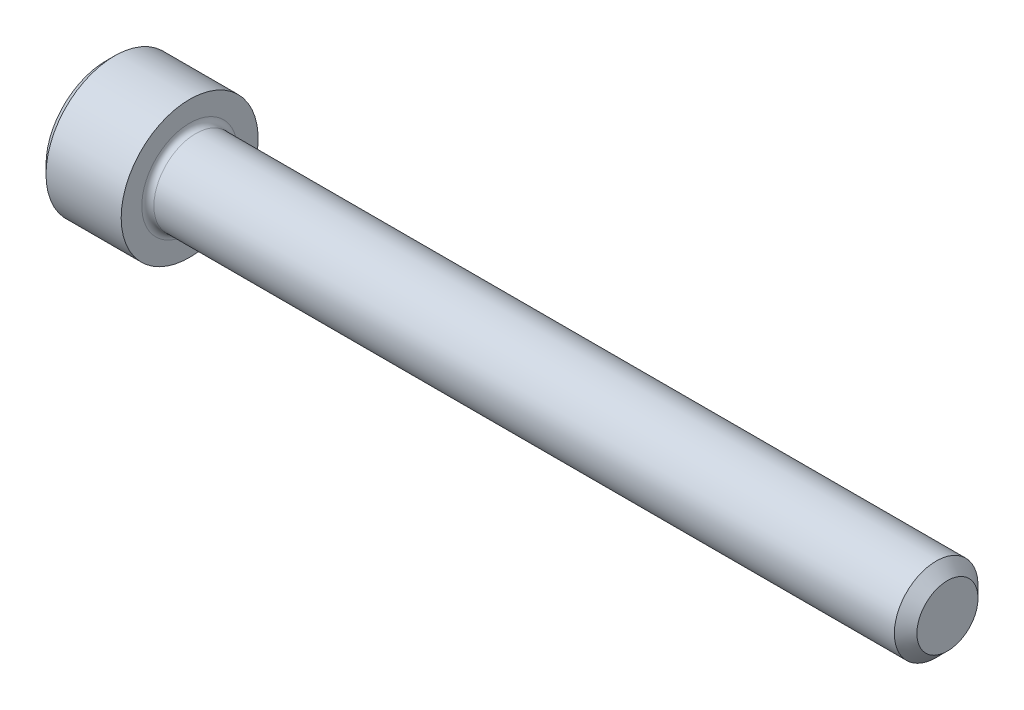
SolidWorks part; units mm, degrees
revolve "Base-Revolve" add sketch "BodySke"
sketch "BodySke" plane through (0, 0, 0) normal (0, 0, 1) x (1, 0, 0)
  line L0 (0, 0) -> (0, 2.5146)
  line L1 (0.3556, 2.8702) -> (3.5052, 2.8702)
  line L2 (3.5052, 2.8702) -> (3.5052, 1.7526)
  line L3 (3.5052, 1.7526) -> (34.7828, 1.7526)
  line L4 (35.2552, 1.2802) -> (35.2552, 0)
  line L5 (35.2552, 0) -> (0, 0)
  line L6 (-31.75, 0) -> (127, 0) construction
  line L7 (0, 2.5146) -> (0.3556, 2.8702)
  line L8 (35.2552, 1.2802) -> (34.7828, 1.7526)
  line L9 (0, -2.5146) -> (0.3556, -2.8702) construction
  line L10 (35.2552, -1.2802) -> (34.7828, -1.7526) construction
  line L11 (4.2977, 9.525) -> (4.2977, 3.175) construction
  line L12 (22.5552, 9.525) -> (22.5552, 3.175) construction
  line L13 (-2.8448, 9.525) -> (-2.8448, 3.175) construction
  dimension "Diameter" = 3.5052
  dimension "Head_ht" = 3.5052
  dimension "Length" = 31.75
  dimension "Body_ch_ang" = 45
  dimension "Head_dia" = 5.7404
  dimension "Head_ch_ang" = 45
  dimension "Head_side_ht" = 3.1496
  dimension "Minor_dia" = 2.5603
  dimension "Advance" = 0.7925
  dimension "Thread_nom" = 12.7
  dimension "Thread_length" = 38.1
cosmetic thread "ThreadCosmetic" [suppressed]
fillet "Fillet1" radius 0.254 1 edges at (3.5052, 0, 1.7526)
ref_plane "Plane1" through (0, 0, 0) normal (0, 0, 1) x (1, 0, 0)
ref_plane "Plane2" through (0, 0, 0) normal (0, 1, 0) x (1, 0, 0)
ref_plane "Plane3" through (0, 0, 0) normal (1, 0, 0) x (0, 0, -1)
sketch "Sketch2" plane through (0, 0, 0) normal (0, 0, 1) x (1, 0, 0)
  line L0 (0, 1.3843) -> (1.6256, 1.3843)
  line L1 (1.6256, 1.3843) -> (2.4248, 0)
  line L2 (-31.75, 0) -> (127, 0) construction
  line L3 (2.4248, 0) -> (0, 0)
  line L4 (0, 0) -> (0, 1.3843)
  line L5 (0, 2.5146) -> (0, -2.5146) construction
  line L6 (0, 0) -> (47.625, 0) construction
  line L7 (3.5052, -2.8702) -> (3.5052, 2.8702) construction
  dimension "D1" = 1.3843
  dimension "D2" = 60
revolve "Hex-PreBroach" cut sketch "Sketch2" angle 360 about L6
sketch "Sketch3" plane through (0, 0, 0) normal (-1, 0, 0) x (0, 0.5, 0.866)
  line L0 (0.7992, 1.3843) -> (-0.7992, 1.3843)
  line L1 (-0.7992, 1.3843) -> (-1.5985, 0)
  line L2 (0.7992, 1.3843) -> (1.5985, 0)
  line L3 (0.7992, -1.3843) -> (1.5985, 0)
  line L4 (0.7992, -1.3843) -> (-0.7992, -1.3843)
  line L5 (-0.7992, -1.3843) -> (-1.5985, 0)
  dimension "D1" = 1.3843
  dimension "D2" = 1.3843
  dimension "Hex_size" = 2.7686
extrude "Hex" cut sketch "Sketch3" against normal blind 1.6256
sketch "Sketch4" plane through (0, 0, 0) normal (-1, 0, 0) x (0, 0, 1)
  line L0 (0, 0) -> (1.7399, 0)
  line L1 (0, 0) -> (6.1484, 3.5498) construction
  line L2 (0, 0) -> (0.8699, 1.5068)
  line L3 (1.4457, 0.3947) -> (1.6607, 0.5189)
  line L4 (1.0647, 1.0546) -> (1.2797, 1.1788)
  arc A0 (1.4457, 0.3947) -> (1.0647, 1.0546) centre (0, 0) ccw
  arc A1 (1.7399, 0) -> (1.6607, 0.5189) centre (0, 0) ccw
  arc A2 (0.8699, 1.5068) -> (1.2797, 1.1788) centre (0, 0) cw
  dimension "D1" = 30
  dimension "D2" = 60
  dimension "Spline_p_dim" = 0.762
  dimension "D3" = 0.381
extrude "Spline" [suppressed] cut sketch "Sketch4" against normal blind 1.6256
pattern_circular "CirPattern1" [suppressed] count 6 every 60
sketch "Sketch5" plane through (0, 0, 0) normal (0, 0, 1) x (1, 0, 0)
  line L0 (-31.75, 0) -> (127, 0) construction
  line L2 (0, 2.5146) -> (0, -2.5146) construction
  circle A0 centre (1.27, 0) radius 0.4445
  dimension "Drilled_hole_dia" = 0.889
  dimension "Drilled_hole_loc" = 1.27
extrude "Hole" [suppressed] cut sketch "Sketch5" against normal through all and the other way through all
pattern_circular "Drilled-4" [suppressed] count 2 every 60
pattern_circular "Drilled-6" [suppressed] count 3 every 60
sketch "ThdSchSke" plane through (0, 0, 0) normal (0, 0, 1) x (1, 0, 0)
  line L0 (22.5552, -1.2802) -> (22.2244, -1.7526)
  line L1 (22.5552, -1.2802) -> (22.886, -1.7526)
  line L2 (22.886, -1.7526) -> (22.886, -2.1907)
  line L3 (-3.175, 0) -> (5.1513, 0) construction
  line L5 (22.886, -2.1907) -> (22.2244, -2.1907)
  line L6 (22.2244, -2.1907) -> (22.2244, -1.7526)
  line L7 (0, 2.5146) -> (0, -2.5146) construction
  dimension "Thread_minor" = 2.5603
  dimension "Diameter" = 3.5052
  dimension "Start" = 22.5552
revolve "ThreadSchematic" [suppressed] cut sketch "ThdSchSke" angle 360 about L3
pattern_linear "ThdSchPat" [suppressed]
equation "\"D2@Sketch3\" = \"Hex_size@Sketch3\" / 2"
equation "\"D1@Sketch3\" = \"Hex_size@Sketch3\" / 2"
equation "\"D1@Sketch2\" = \"Hex_size@Sketch3\" / 2"
equation "\"D3@Sketch4\" = \"Spline_p_dim@Sketch4\" / 2"
equation "\"Thread_minor@ThreadCosmetic\"  =  \"Minor_dia@BodySke\""
equation "\"D2@CirPattern1\" = 360 / \"Num_teeth@CirPattern1\""
equation "\"Wall_thickness@Sketch2\" = \"Head_ht@BodySke\" - \"Key_eng@Hex\""
equation "\"Thread_length@ThreadCosmetic\" = ((sgn( (\"Length@BodySke\" - \"Advance@BodySke\" ) - \"Thread_nom@BodySke\" )-1)*( (\"Length@BodySke\" - \"Advance@BodySke\" ) - \"Thread_nom@BodySke\" ))/-2+ \"Thread_nom@BodySke\""
equation "\"Thread_minor@ThdSchSke\" = \"Minor_dia@BodySke\""
equation "\"Diameter@ThdSchSke\" = \"Diameter@BodySke\""
equation "\"Overcut@ThdSchSke\" = \"Diameter@BodySke\" * 1.25"
equation "\"Start@ThdSchSke\" = \"Head_ht@BodySke\" + \"Length@BodySke\" - \"Thread_length@ThreadCosmetic\"  '---Non-countersunk---"
equation "\"Num_threads@ThdSchPat\" = int( \"Thread_length@ThreadCosmetic\" / \"Advance@BodySke\" + 0.999 )  + 1"
equation "\"Advance@ThdSchPat\" = \"Thread_length@ThreadCosmetic\" /  (\"Num_threads@ThdSchPat\" - 1) 'relax it"
equation "\"Num_threads@ThdSchPat\" = \"Num_threads@ThdSchPat\" - sgn( \"Num_threads@ThdSchPat\" - 1) '---chamfered tips only---"
